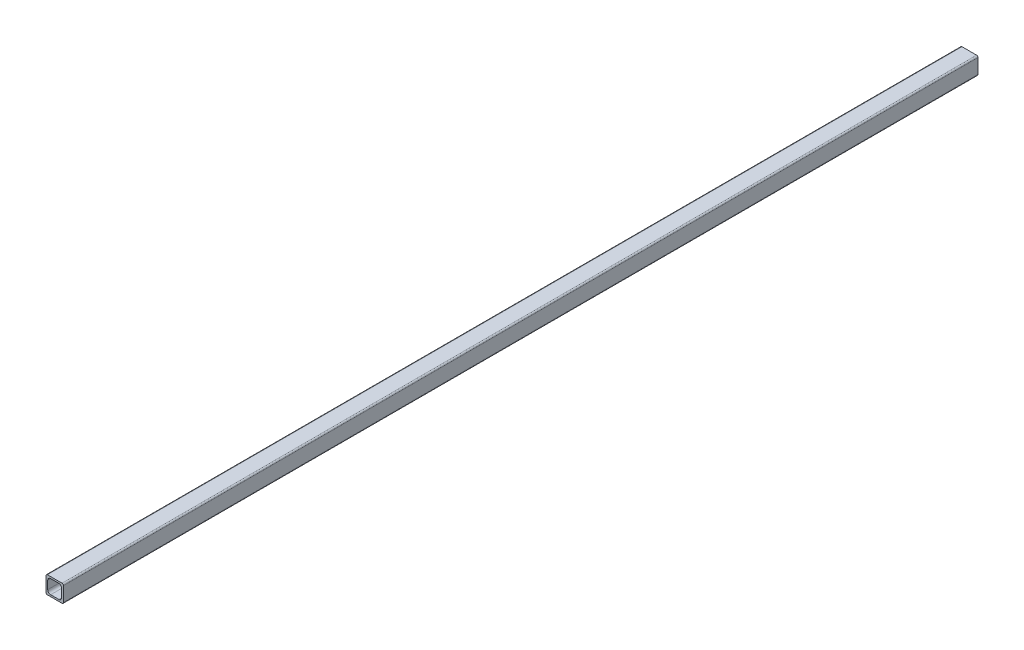
SolidWorks part; units mm, degrees
ref_plane "Front Plane" through (0, 0, 0) normal (0, 0, 1) x (1, 0, 0)
ref_plane "Top Plane" through (0, 0, 0) normal (0, 1, 0) x (1, 0, 0)
ref_plane "Right Plane" through (0, 0, 0) normal (1, 0, 0) x (0, 0, -1)
sketch "Sketch1" plane through (0, 0, 0) normal (0, 0, 1) x (1, 0, 0)
  line L1 (1.524, 0) -> (17.526, 0)
  line L2 (0, 1.524) -> (0, 17.526)
  line L3 (1.524, 19.05) -> (17.526, 19.05)
  line L4 (19.05, 1.524) -> (19.05, 17.526)
  arc A0 (0, 1.524) -> (1.524, 0) centre (1.524, 1.524) ccw
  arc A1 (17.526, 0) -> (19.05, 1.524) centre (17.526, 1.524) ccw
  arc A2 (19.05, 17.526) -> (17.526, 19.05) centre (17.526, 17.526) ccw
  arc A3 (0, 17.526) -> (1.524, 19.05) centre (1.524, 17.526) cw
  point P7 (0, 0)
  point P10 (19.05, 0)
  point P13 (19.05, 19.05)
  point P16 (0, 19.05)
  dimension "D3" = 1.524
  dimension "D1" = 19.05
  dimension "D2" = 19.05
extrude "Boss-Extrude1" add sketch "Sketch1" against normal blind 1000.125
sketch "Sketch2" plane through (0, 0, 0) normal (0, 0, 1) x (1, 0, 0)
  line L0 (19.05, 1.524) -> (19.05, 17.526) construction
  line L1 (5.08, 17.145) -> (13.97, 17.145)
  line L2 (1.905, 13.97) -> (1.905, 5.08)
  line L3 (5.08, 1.905) -> (13.97, 1.905)
  line L4 (17.145, 13.97) -> (17.145, 5.08)
  line L5 (17.526, 19.05) -> (1.524, 19.05) construction
  line L6 (1.524, 0) -> (17.526, 0) construction
  arc A0 (13.97, 17.145) -> (17.145, 13.97) centre (13.97, 13.97) cw
  arc A1 (17.145, 5.08) -> (13.97, 1.905) centre (13.97, 5.08) cw
  arc A2 (5.08, 1.905) -> (1.905, 5.08) centre (5.08, 5.08) cw
  arc A3 (1.905, 13.97) -> (5.08, 17.145) centre (5.08, 13.97) cw
  point P12 (17.145, 17.145)
  point P15 (17.145, 1.905)
  point P18 (1.905, 1.905)
  dimension "D6" = 3.175
  dimension "D1" = 15.24
  dimension "D2" = 15.24
  dimension "D3" = 1.905
  dimension "D4" = 1.905
  dimension "D5" = 1.905
extrude "Cut-Extrude1" cut sketch "Sketch2" against normal through all
